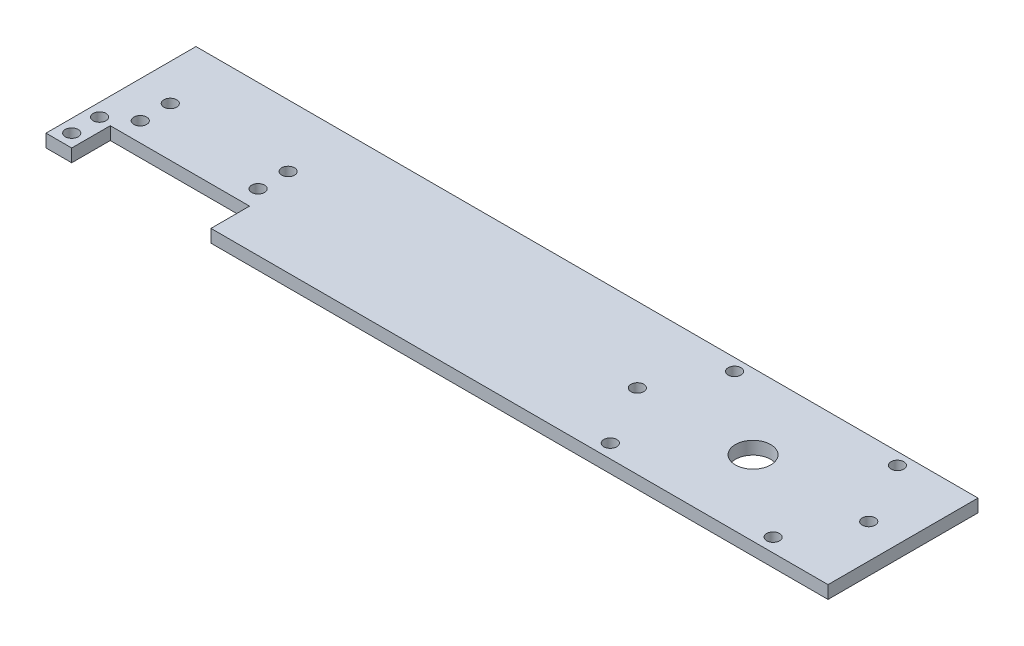
SolidWorks part; units mm, degrees
ref_plane "Front Plane" through (0, 0, 0) normal (0, 0, 1) x (1, 0, 0)
ref_plane "Top Plane" through (0, 0, 0) normal (0, 1, 0) x (1, 0, 0)
ref_plane "Right Plane" through (0, 0, 0) normal (1, 0, 0) x (0, 0, -1)
sketch "Sketch1" plane through (0, 0, 0) normal (0, 1, 0) x (1, 0, 0)
  line L0 (47.5, 13.6856) -> (47.5, -3.2344) construction
  line L1 (-100, 22.5) -> (82.5, 22.5)
  line L2 (-100, 22.5) -> (-100, -12.5)
  line L3 (-100, -12.5) -> (82.5, -12.5)
  line L4 (82.5, 22.5) -> (82.5, -12.5)
  line L6 (12.5, -1) -> (82.5, -1)
  line L7 (12.5, -1) -> (12.5, 11)
  line L8 (12.5, 11) -> (82.5, 11)
  line L9 (82.5, -1) -> (82.5, 11)
  line L10 (12.5, -1) -> (82.5, 11) construction
  line L11 (12.5, 11) -> (82.5, -1) construction
  circle A4 centre (47.5, 5) radius 4.125
  circle A5 centre (74.5, 5) radius 1.5
  circle A6 centre (20.5, 5) radius 1.5
  circle A7 centre (-97, -9.5) radius 1.5
  circle A8 centre (-97, -3) radius 1.5
  circle A9 centre (-91.5, 8) radius 1.5
  circle A10 centre (-64, 8) radius 1.5
  circle A11 centre (-64, 1) radius 1.5
  circle A12 centre (-91.5, 1) radius 1.5
  point P0 (0, 0)
  dimension "D3" = 3
  dimension "D4" = 8.25
  dimension "D5" = 3
  dimension "D9" = 3
  dimension "D13" = 3
  dimension "D1" = 35
  dimension "D2" = 182.5
  dimension "D6" = 8
  dimension "D7" = 70
  dimension "D8" = 12
  dimension "D10" = 3
  dimension "D11" = 6.5
  dimension "D12" = 3
  dimension "D14" = 14.5
  dimension "D15" = 8.5
  dimension "D18" = 27.5
  dimension "D16" = 2
  dimension "D17" = 2
extrude "Boss-Extrude1" add sketch "Sketch1" along normal blind 3 contours L7 L8 L4 L1 L2 L3 L6 | L8 L7 L6 L4 A4 A5 A6
sketch "Sketch2" plane through (0, 0, 0) normal (0, 0, 1) x (1, 0, 0)
  line L0 (-94.5, 33) -> (-94.5, -17) construction
  line L1 (-92, 33) -> (-92, -17)
  line L2 (-97, 33) -> (-97, -17)
  line L3 (-89, 33) -> (-89, -17)
  line L4 (-100, 33) -> (-100, -17)
  line L5 (-100, 3) -> (-100, 0) construction
  line L7 (-94, 6.4998) -> (-61.5, 6.4998)
  line L8 (-94, 6.4998) -> (-94, -3.3981)
  line L9 (-94, -3.3981) -> (-61.5, -3.3981)
  line L10 (-61.5, 6.4998) -> (-61.5, -3.3981)
  arc A0 (-92, 33) -> (-97, 33) centre (-94.5, 33) ccw
  arc A1 (-97, -17) -> (-92, -17) centre (-94.5, -17) ccw
  arc A2 (-100, -17) -> (-89, -17) centre (-94.5, -17) ccw
  arc A3 (-89, 33) -> (-100, 33) centre (-94.5, 33) ccw
  point P2 (-94.5, 8)
  dimension "D4" = 5.5
  dimension "D1" = 3
  dimension "D2" = 3
  dimension "D3" = 5
  dimension "D5" = 50
  dimension "D6" = 50
  dimension "D7" = 6
  dimension "D8" = 32.5
extrude "Cut-Extrude3" cut sketch "Sketch2" along normal up to surface (9 mm away) from offset 3.5 contours L1 L9 L3 L7 | L10 L7 L3 L9 | L8 L9 L1 L7 up to face at (-8.75, 1.5, 12.5)
ref_plane "Plane3" through (0, 3, 0) normal (0, -1, 0) x (-1, 0, 0)
sketch "Sketch3" plane through (0, 3, 0) normal (0, -1, 0) x (-1, 0, 0)
  line L0 (-82.5, -12.5) -> (-20.5, -12.5)
  line L2 (-20.5, 5) -> (-20.5, -12.5) construction
  line L3 (-74.5, 5) -> (-74.5, -12.5) construction
  line L5 (-69.5043, 22.7064) -> (-69.5043, -12.2936)
  line L6 (-37.5, -12.5) -> (25.1934, -12.5) construction
  line L7 (-20.5, -12.5) -> (-20.5, 22.5)
  line L8 (100, 22.5) -> (-82.5, 22.5) construction
  line L9 (-20.5, 22.5) -> (-82.5, 22.5)
  line L10 (-25.5, 22.5) -> (-25.5, -12.5)
  line L11 (-69.5043, 22.7064) -> (-25.5, 22.5)
  line L12 (-69.5043, -12.2936) -> (-25.5, -12.5)
  circle A4 centre (-66.5, -9.3076) radius 1.5
  circle A5 centre (-28.5, -9.3076) radius 1.5
  circle A6 centre (-28.5, 19.6924) radius 1.5
  circle A7 centre (-66.5, 19.6924) radius 1.5
  point P14 (-69.5043, 5.2064)
  dimension "D3" = 35
  dimension "D4" = 5
  dimension "D8" = 8
  dimension "D1" = 54
  dimension "D2" = 5
  dimension "D5" = 62
  dimension "D6" = 54
  dimension "D7" = 44.0043
  dimension "D9" = 3.0043
  dimension "D10" = 3
  dimension "D13" = 3
  dimension "D11" = 2
  dimension "D12" = 2
extrude "Cut-Extrude7" cut sketch "Sketch3" along normal blind 10 contours A4 | A7 | A6 | A5
